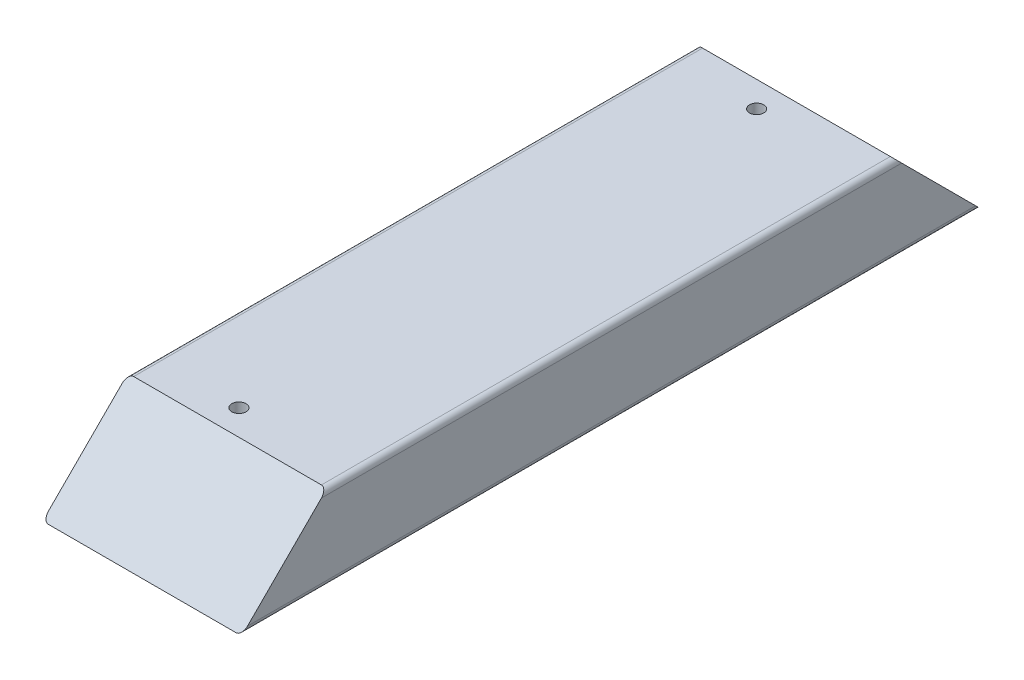
SolidWorks part; units mm, degrees
ref_plane "Front Plane" through (0, 0, 0) normal (0, 0, 1) x (1, 0, 0)
ref_plane "Top Plane" through (0, 0, 0) normal (0, 1, 0) x (1, 0, 0)
ref_plane "Right Plane" through (0, 0, 0) normal (1, 0, 0) x (0, 0, -1)
sketch "Sketch1" plane through (0, 0, 0) normal (0, 0, 1) x (1, 0, 0)
  line L1 (-44.45, 19.05) -> (44.45, 19.05)
  line L2 (-44.45, 19.05) -> (-44.45, -19.05)
  line L3 (-44.45, -19.05) -> (44.45, -19.05)
  line L4 (44.45, 19.05) -> (44.45, -19.05)
  line L5 (-44.45, 19.05) -> (44.45, -19.05) construction
  line L6 (-44.45, -19.05) -> (44.45, 19.05) construction
  point P0 (0, 0)
  dimension "D1" = 88.9
  dimension "D2" = 38.1
extrude "Boss-Extrude1" add sketch "Sketch1" along normal blind 330.2
fillet "Fillet1" radius 2.54 4 edges at (-44.45, -19.05, 165.1) (44.45, -19.05, 165.1) (44.45, 19.05, 165.1) (-44.45, 19.05, 165.1)
sketch "Sketch2" plane through (-44.45, 0, 0) normal (-1, 0, 0) x (0, 0, 1)
  line L0 (0, 19.05) -> (0, -19.05)
  line L1 (330.2, -19.05) -> (0, -19.05) construction
  line L2 (0, -16.51) -> (0, -19.05) construction
  line L3 (0, -19.05) -> (38.1, 19.05)
  line L4 (0, 19.05) -> (330.2, 19.05) construction
  line L5 (38.1, 19.05) -> (0, 19.05)
  dimension "D1" = 45
extrude "Cut-Extrude1" cut sketch "Sketch2" against normal blind 406.4
ref_plane "Plane1" through (0, 0, 165.1) normal (0, 0, 1) x (1, 0, 0)
mirror "Mirror1" about plane through (0, 0, 165.1) normal (0, 0, 1) of "Cut-Extrude1"
sketch "Sketch3" plane through (0, 19.05, 0) normal (0, 1, 0) x (1, 0, 0)
  line L1 (41.91, -38.1) -> (-41.91, -38.1) construction
  line L2 (-41.91, 0) -> (41.91, 0) construction
  circle A0 centre (-6.35, -49.53) radius 3.175
  point P2 (0, 0)
  dimension "D2" = 6.35
  dimension "D1" = 6.35
  dimension "D3" = 11.43
extrude "Cut-Extrude2" cut sketch "Sketch3" against normal blind 12.7
mirror "Mirror4" about plane through (0, 0, 165.1) normal (0, 0, 1) of "Cut-Extrude2"
